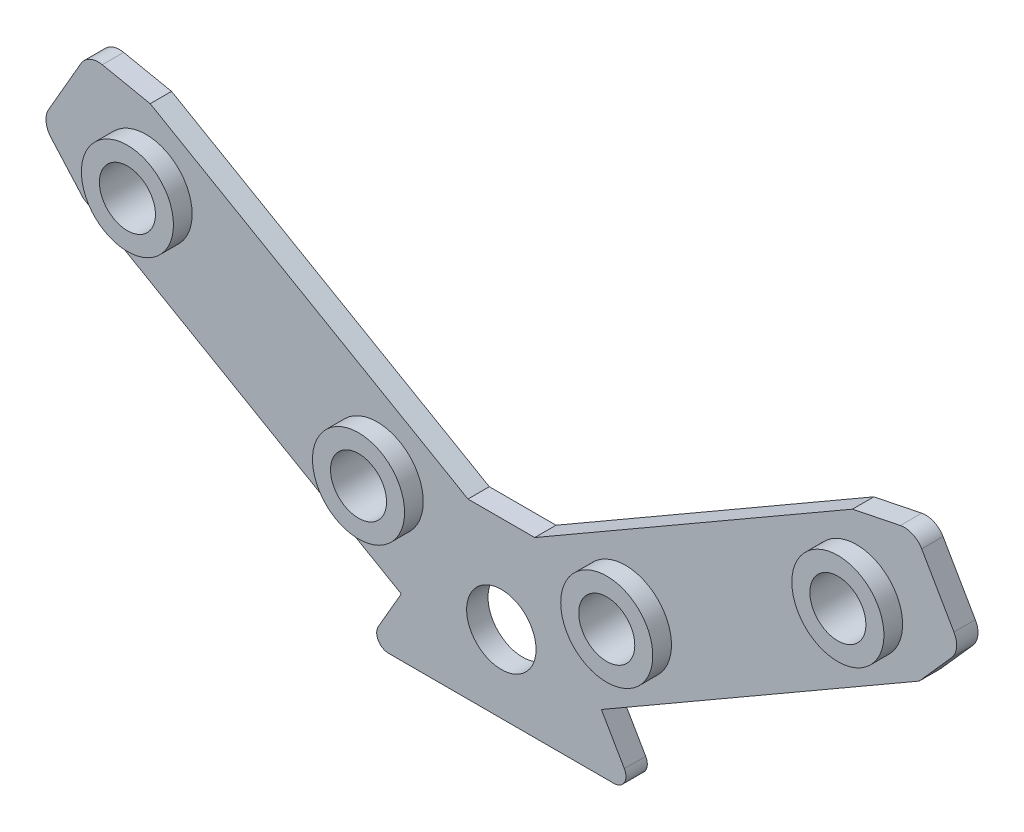
SolidWorks part; units mm, degrees
material "Plain Carbon Steel"
ref_plane "Front Plane" through (0, 0, 0) normal (0, 0, 1) x (1, 0, 0)
ref_plane "Top Plane" through (0, 0, 0) normal (0, 1, 0) x (1, 0, 0)
ref_plane "Right Plane" through (0, 0, 0) normal (1, 0, 0) x (0, 0, -1)
sketch "Sketch1" plane through (0, 0, 0) normal (0, 0, 1) x (1, 0, 0)
  line L0 (0, 0) -> (0, 67.9164) construction
  line L1 (-2.5, 7.2169) -> (2.5, 7.2169)
  line L2 (2.5, 7.2169) -> (26.3157, 20.9669)
  line L3 (26.3157, 20.9669) -> (29.9036, 21.7011)
  line L4 (31.5034, 20.9815) -> (33.9222, 16.792)
  line L5 (32.7128, 18.8868) -> (0, 0) construction
  line L6 (31.3157, 12.3066) -> (33.7455, 15.0468)
  line L7 (7.5, -1.4434) -> (31.3157, 12.3066)
  line L8 (7.5, -1.4434) -> (9.2206, -4.4235)
  line L9 (8.4412, -5.7735) -> (-8.4412, -5.7735)
  line L12 (-7.5, -1.4434) -> (-9.2206, -4.4235)
  line L13 (-7.5, -1.4434) -> (-31.3157, 12.3066)
  line L14 (-31.3157, 12.3066) -> (-33.7455, 15.0468)
  line L15 (-31.5034, 20.9815) -> (-33.9222, 16.792)
  line L16 (-26.3157, 20.9669) -> (-29.9036, 21.7011)
  line L17 (-2.5, 7.2169) -> (-26.3157, 20.9669)
  circle A0 centre (0, 0) radius 2.6
  arc A1 (-33.7455, 15.0468) -> (-33.9222, 16.792) centre (-32.6232, 16.042) cw
  arc A2 (-31.5034, 20.9815) -> (-29.9036, 21.7011) centre (-30.2043, 20.2315) cw
  arc A3 (29.9036, 21.7011) -> (31.5034, 20.9815) centre (30.2043, 20.2315) cw
  arc A4 (33.7455, 15.0468) -> (33.9222, 16.792) centre (32.6232, 16.042) ccw
  arc A5 (-9.2206, -4.4235) -> (-8.4412, -5.7735) centre (-8.4412, -4.8735) ccw
  arc A6 (9.2206, -4.4235) -> (8.4412, -5.7735) centre (8.4412, -4.8735) cw
  point P13 (-10, -5.7735)
  point P17 (10, -5.7735)
  point P24 (0, 7.2169)
  point P26 (-34.4628, 15.8557)
  point P29 (-30.9628, 21.9178)
  point P32 (30.9628, 21.9178)
  point P35 (34.4628, 15.8557)
  dimension "D4" = 5
  dimension "D8" = 5
  dimension "D9" = 0.9
  dimension "D11" = 1.5
  dimension "D1" = 5.2
  dimension "D2" = 10
  dimension "D3" = 60
  dimension "D5" = 32
  dimension "D6" = 4.5
  dimension "D7" = 7
extrude "Boss-Extrude1" add sketch "Sketch1" along normal blind 1.6
sketch "Sketch2" plane through (0, 0, 1.6) normal (0, 0, 1) x (1, 0, 0)
  line L0 (-32.7128, 18.8868) -> (-6.8828, 3.9738) construction
  line L1 (-31.5034, 20.9815) -> (-33.9222, 16.792) construction
  line L2 (0, 7.2169) -> (0, 26.5175) construction
  line L5 (-2.5, 7.2169) -> (-26.3157, 20.9669) construction
  line L8 (2.5, 7.2169) -> (-2.5, 7.2169) construction
  line L9 (-9.3011, 5.37) -> (-11.8011, 1.0399) construction
  line L10 (-31.3157, 12.3066) -> (-7.5, -1.4434) construction
  circle A0 centre (26.6216, 15.37) radius 3.45
  circle A1 centre (9.3011, 5.37) radius 3.45
  circle A4 centre (-9.3011, 5.37) radius 3.45
  circle A5 centre (-26.6216, 15.37) radius 3.45
  dimension "D1" = 6.9
  dimension "D2" = 10.74
  dimension "D4" = 20
extrude "Boss-Extrude2" add sketch "Sketch2" along normal blind 1.4
hole_wizard "M5x0.8 Tapped Hole1" positions "Sketch4" profile "Sketch3" tap size "M5x0.8" standard "ANSI Metric" end condition through all
sketch "Sketch4" plane through (0, 0, 3) normal (0, 0, 1) x (1, 0, 0)
  point P0 (26.6216, 15.37)
  point P3 (9.3011, 5.37)
  point P13 (-9.3011, 5.37)
  point P16 (-26.6216, 15.37)
cosmetic thread "Hole Thread3" parameters "D2"=5
cosmetic thread "Hole Thread5" parameters "D2"=5
cosmetic thread "Hole Thread6" parameters "D2"=5
cosmetic thread "Hole Thread7" parameters "D2"=5
sketch "Sketch3" plane through (26.6216, 15.37, 3) normal (1, 0, 0) x (0, -1, 0)
  line L0 (0, 0) -> (0, 3)
  line L1 (0, 3) -> (2.1, 3)
  line L2 (2.1, 3) -> (2.1, 0)
  line L5 (2.1, 0) -> (0, 0)
  line L11 (0, -6.35) -> (0, 107.95) construction
  dimension "Thru Tap Drill Dia." = 4.2
  dimension "Thru Tap Drill Depth" = 3
